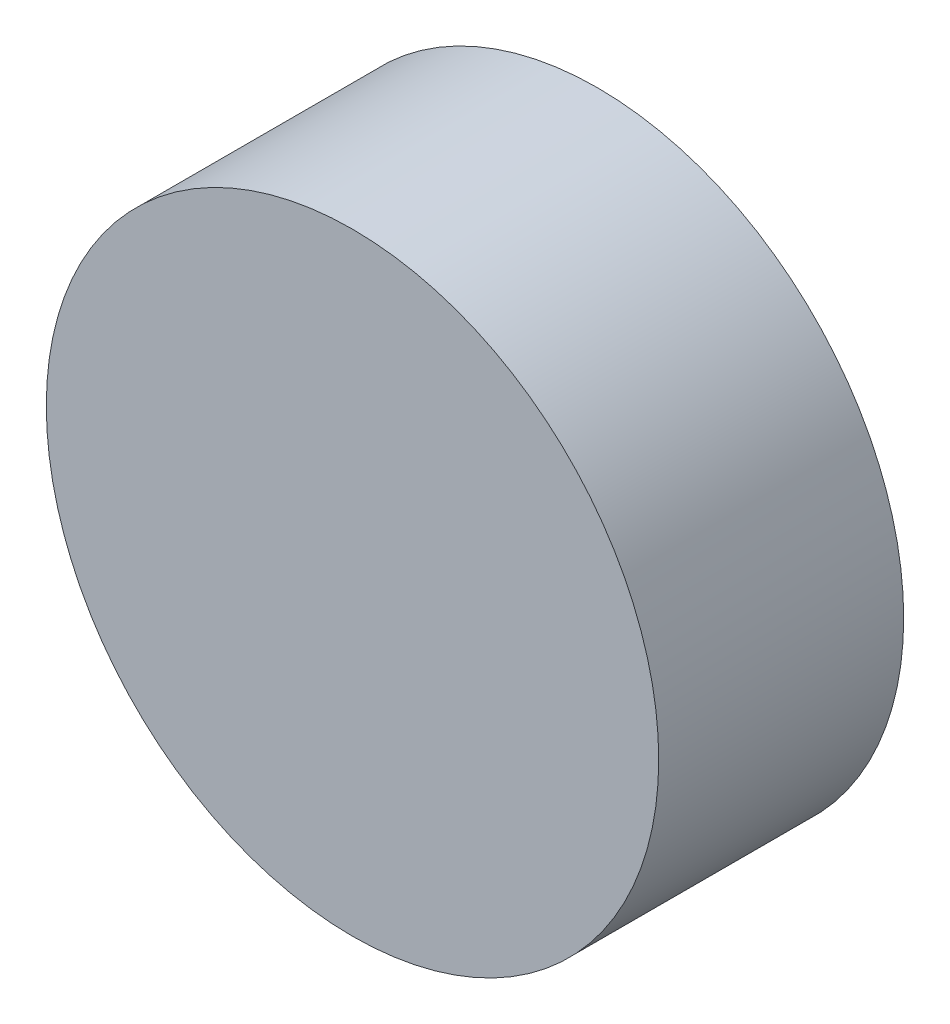
SolidWorks part; units mm, degrees
ref_plane "Front Plane" through (0, 0, 0) normal (0, 0, 1) x (1, 0, 0)
ref_plane "Top Plane" through (0, 0, 0) normal (0, 1, 0) x (1, 0, 0)
ref_plane "Right Plane" through (0, 0, 0) normal (1, 0, 0) x (0, 0, -1)
sketch "Sketch1" plane through (0, 0, 0) normal (0, 0, 1) x (1, 0, 0)
  circle A0 centre (0, 0) radius 250
  dimension "D1" = 500
extrude "Boss-Extrude2" add sketch "Sketch1" along normal blind 200
